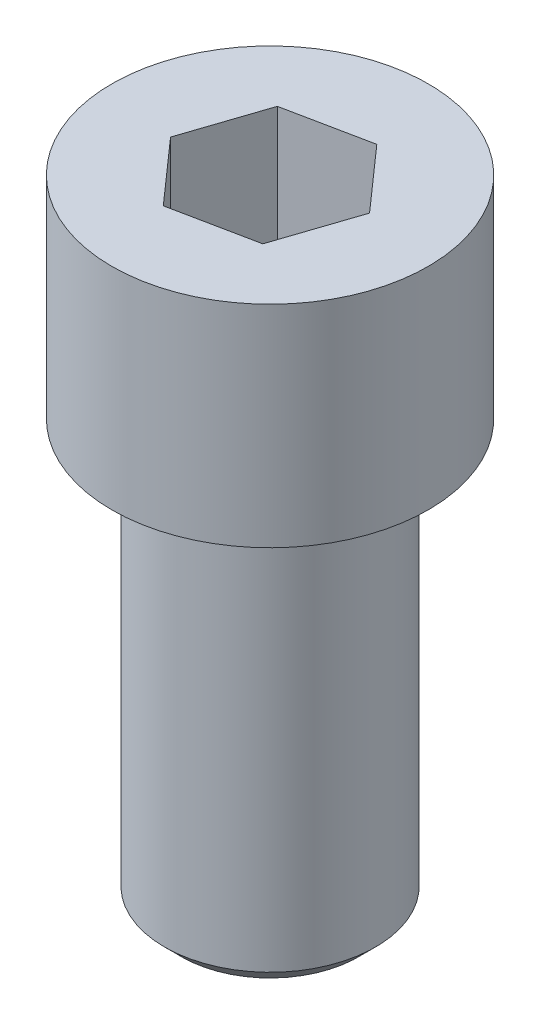
SolidWorks part; units mm, degrees
ref_plane "Front Plane" through (0, 0, 0) normal (0, 0, 1) x (1, 0, 0)
ref_plane "Top Plane" through (0, 0, 0) normal (0, 1, 0) x (1, 0, 0)
ref_plane "Right Plane" through (0, 0, 0) normal (1, 0, 0) x (0, 0, -1)
sketch "Sketch1" plane through (0, 0, 0) normal (0, 1, 0) x (1, 0, 0)
  circle A0 centre (0, 0) radius 1.875
  dimension "D1" = 3.75
extrude "Boss-Extrude1" add sketch "Sketch1" along normal blind 2.5
sketch "Sketch2" plane through (0, 0, 0) normal (0, -1, 0) x (-1, 0, 0)
  circle A0 centre (0, 0) radius 1.25
  dimension "D1" = 2.5
extrude "Boss-Extrude2" add sketch "Sketch2" along normal blind 5
fillet "Fillet1" radius 0.15 1 edges at (0, 0, -1.25)
chamfer "Chamfer1" distance 0.2 angle 45 1 edges at (0, -5, -1.25)
sketch "Sketch3" plane through (0, 2.5, 0) normal (0, 1, 0) x (1, 0, 0)
  line L1 (-0.9799, -0.1994) -> (-0.3172, -0.9484)
  line L2 (-0.3172, -0.9484) -> (0.6627, -0.7489)
  line L3 (0.6627, -0.7489) -> (0.9799, 0.1994)
  line L4 (0.9799, 0.1994) -> (0.3172, 0.9484)
  line L5 (0.3172, 0.9484) -> (-0.6627, 0.7489)
  line L6 (-0.6627, 0.7489) -> (-0.9799, -0.1994)
  circle A0 centre (0, 0) radius 0.866 construction
  dimension "D1" = 2
extrude "Cut-Extrude1" cut sketch "Sketch3" against normal blind 1.5
